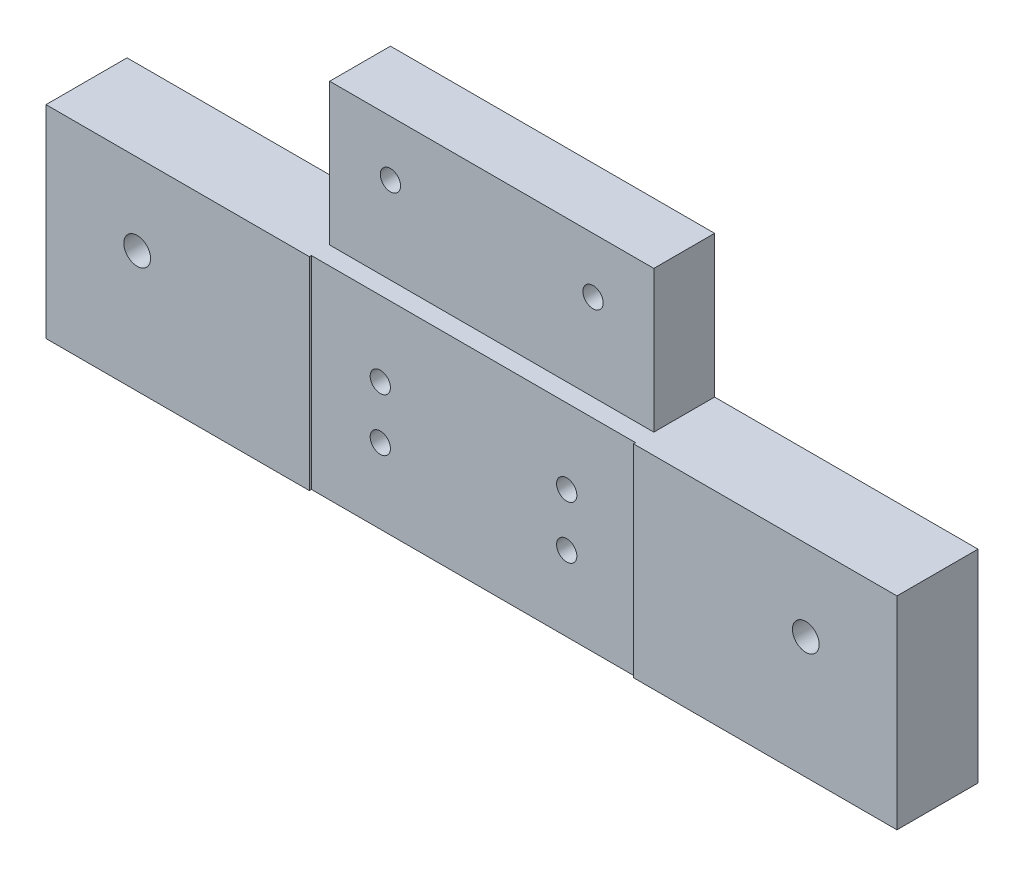
SolidWorks part; units mm, degrees
material "1023 Листовая углеродистая сталь (SS)"
ref_plane "Front" through (0, 0, 0) normal (0, 0, 1) x (1, 0, 0)
ref_plane "Top" through (0, 0, 0) normal (0, 1, 0) x (1, 0, 0)
ref_plane "Right" through (0, 0, 0) normal (1, 0, 0) x (0, 0, -1)
sketch "Sketch1" plane through (0, 0, 0) normal (0, 0, 1) x (1, 0, 0)
  line L1 (-105, 25) -> (105, 25)
  line L2 (-105, 25) -> (-105, -25)
  line L3 (-105, -25) -> (105, -25)
  line L4 (105, 25) -> (105, -25)
  line L5 (-105, 25) -> (105, -25) construction
  line L6 (-105, -25) -> (105, 25) construction
  point P0 (0, 0)
  dimension "D1" = 50
  dimension "D2" = 210
extrude "Extrude1" add sketch "Sketch1" along normal blind 20
hole_wizard "CBORE for M6 Hex Head Flange Bolt1" positions "Sketch2" profile "Sketch3" counterbore size "M6" standard "DIN" end condition through all
sketch "Sketch2" plane through (0, 0, 0) normal (0, 0, -1) x (-1, 0, 0)
  line L0 (-82.5, 5) -> (82.5, 5)
  line L1 (0, 5) -> (0, 0) construction
  point P0 (82.5, 5)
  point P2 (-82.5, 5)
  dimension "D1" = 165
  dimension "D2" = 5
sketch "Sketch3" plane through (-82.5, 5, 0) normal (1, 0, 0) x (0, 1, 0)
  line L0 (0, 0) -> (0, 20)
  line L1 (0, 20) -> (3.3, 20)
  line L3 (3.3, 20) -> (3.3, 6.6)
  line L4 (3.3, 6.6) -> (8, 6.6)
  line L5 (8, 6.6) -> (8, 0)
  line L7 (8, 0) -> (0, 0)
  line L11 (0, -6.35) -> (0, 107.95) construction
  dimension "Диаметр сквозного отверстия" = 6.6
  dimension "Глубина сквозного отверстия" = 20
  dimension "Диаметр цековки" = 16
  dimension "Глубина цековки" = 6.6
sketch "Sketch4" plane through (0, 25, 0) normal (0, 1, 0) x (1, 0, 0)
  line L0 (105, -20) -> (-105, -20) construction
  line L1 (-40, -19.5) -> (40, -19.5)
  line L2 (-40, -19.5) -> (-40, -20)
  line L3 (-40, -20) -> (40, -20)
  line L4 (40, -19.5) -> (40, -20)
  line L5 (0, -19.5) -> (0, 0) construction
  dimension "D1" = 0.5
  dimension "D2" = 80
extrude "Cut-Extrude1" cut sketch "Sketch4" against normal up to next
hole_wizard "M6 Tapped Hole1" positions "Sketch5" profile "Sketch6" tap size "M6" standard "DIN" end condition through all
sketch "Sketch5" plane through (0, 0, 19.5) normal (0, 0, 1) x (1, 0, 0)
  point P0 (-23, 6.5)
  point P3 (-23, -6.5)
  point P6 (23, 6.5)
  point P9 (23, -6.5)
sketch "Sketch6" plane through (-23, 6.5, 19.5) normal (1, 0, 0) x (0, -1, 0)
  line L0 (0, 0) -> (0, 19.5)
  line L1 (0, 19.5) -> (2.5, 19.5)
  line L2 (2.5, 19.5) -> (2.5, 0)
  line L5 (2.5, 0) -> (0, 0)
  line L11 (0, -6.35) -> (0, 107.95) construction
  dimension "Диаметр проходного сверла" = 5
  dimension "Глубина проходного сверла" = 19.5
cosmetic thread "Cosmetic Thread1" parameters "D2"=6
cosmetic thread "Cosmetic Thread2" parameters "D2"=6
cosmetic thread "Cosmetic Thread3" parameters "D2"=6
cosmetic thread "Cosmetic Thread4" parameters "D2"=6
sketch "Sketch7" plane through (0, 0, 19.5) normal (0, 0, 1) x (1, 0, 0)
  line L2 (-40, 25) -> (40, 25)
  line L3 (-40, 25) -> (-40, 60)
  line L4 (-40, 60) -> (40, 60)
  line L5 (40, 25) -> (40, 60)
  dimension "D1" = 35
  dimension "D2" = 80
extrude "Extrude2" add sketch "Sketch7" against normal up to surface (19.5 mm away) up to face at (-20.5, 6.5, 0)
sketch "Sketch8" plane through (0, 60, 0) normal (0, 1, 0) x (1, 0, 0)
  line L1 (-40, -20) -> (40, -20)
  line L2 (-40, -20) -> (-40, -15)
  line L3 (-40, -15) -> (40, -15)
  line L4 (40, -20) -> (40, -15)
  dimension "D1" = 5
  dimension "D2" = 80
extrude "Cut-Extrude2" cut sketch "Sketch8" against normal up to surface (35 mm away) up to face at (-66, 25, 11.9)
hole_wizard "M6 Tapped Hole2" positions "Sketch9" profile "Sketch10" tap size "M6" standard "DIN" end condition through all
sketch "Sketch9" plane through (0, 0, 15) normal (0, 0, 1) x (1, 0, 0)
  point P0 (-25, 46.3594)
  point P3 (25, 46.3594)
sketch "Sketch10" plane through (-25, 46.3594, 15) normal (1, 0, 0) x (0, -1, 0)
  line L0 (0, 0) -> (0, 15)
  line L1 (0, 15) -> (2.5, 15)
  line L2 (2.5, 15) -> (2.5, 0)
  line L5 (2.5, 0) -> (0, 0)
  line L11 (0, -6.35) -> (0, 107.95) construction
  dimension "Диаметр проходного сверла" = 5
  dimension "Глубина проходного сверла" = 15
cosmetic thread "Cosmetic Thread5" parameters "D2"=6
cosmetic thread "Cosmetic Thread6" parameters "D2"=6
